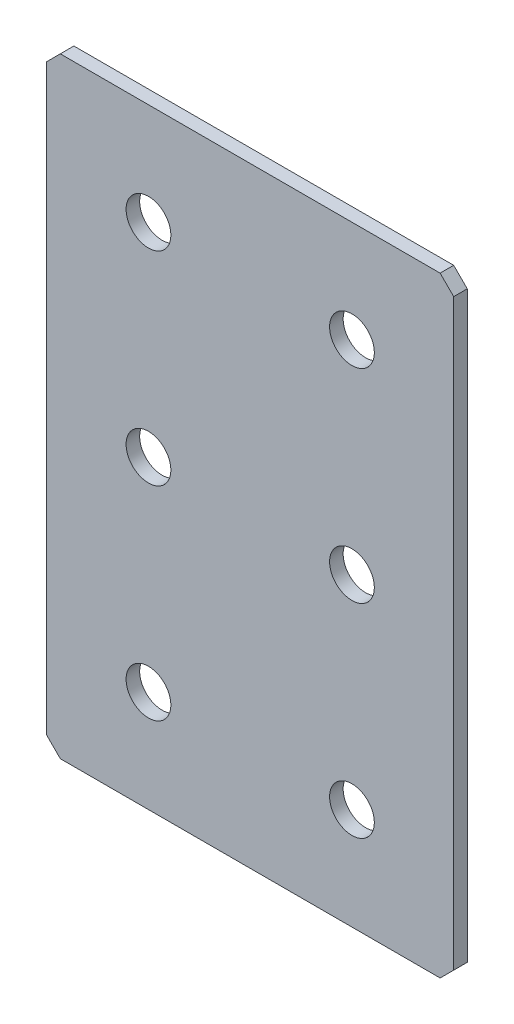
SolidWorks part; units mm, degrees
material "Простая углеродистая сталь"
ref_plane "Спереди(Плоскость XY)" through (0, 0, 0) normal (0, 0, 1) x (1, 0, 0)
ref_plane "Сверху(Плоскость XZ)" through (0, 0, 0) normal (0, 1, 0) x (1, 0, 0)
ref_plane "Справа(Плоскость ZY)" through (0, 0, 0) normal (1, 0, 0) x (0, 0, -1)
sketch "Эскиз1" plane through (0, 0, 0) normal (0, 0, 1) x (1, 0, 0)
  line L1 (-30, -45) -> (30, -45)
  line L2 (-30, -45) -> (-30, 45)
  line L3 (-30, 45) -> (30, 45)
  line L4 (30, -45) -> (30, 45)
  line L5 (-30, -45) -> (30, 45) construction
  line L6 (-30, 45) -> (30, -45) construction
  point P0 (0, 0)
  dimension "D1" = 60
  dimension "D2" = 90
extrude "Бобышка-Вытянуть1" add sketch "Эскиз1" along normal blind 2
chamfer "Фаска1" distance 2 angle 45 4 edges at (-30, -45, 1) (30, -45, 1) (-30, 45, 1) (30, 45, 1)
hole_wizard "Отверстие с зазором M61" positions "Эскиз2" profile "Эскиз3" hole size "M6" standard "DIN" end condition through all
sketch "Эскиз2" plane through (0, 0, 2) normal (0, 0, 1) x (1, 0, 0)
  line L0 (15, 0) -> (-15, 0) construction
  point P0 (-15, 30)
  point P2 (15, 30)
  point P4 (15, 0)
  point P6 (-15, 0)
  point P8 (-15, -30)
  point P10 (15, -30)
  dimension "D1" = 30
  dimension "D2" = 30
  dimension "D3" = 30
sketch "Эскиз3" plane through (-15, 30, 2) normal (1, 0, 0) x (0, -1, 0)
  line L0 (0, 0) -> (0, 2)
  line L1 (0, 2) -> (3.3, 2)
  line L2 (3.3, 2) -> (3.3, 0)
  line L5 (3.3, 0) -> (0, 0)
  line L11 (0, -6.35) -> (0, 107.95) construction
  dimension "Диаметр сквозного отверстия" = 6.6
  dimension "Глубина сквозного отверстия" = 2
